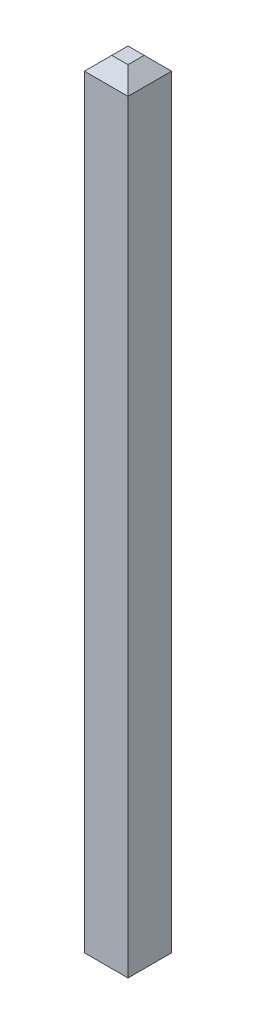
SolidWorks part; units mm, degrees
ref_plane "Alzado" through (0, 0, 0) normal (0, 0, 1) x (1, 0, 0)
ref_plane "Planta" through (0, 0, 0) normal (0, 1, 0) x (1, 0, 0)
ref_plane "Vista lateral" through (0, 0, 0) normal (1, 0, 0) x (0, 0, -1)
sketch "pin_drawing" plane through (0, 0, 0) normal (0, 1, 0) x (1, 0, 0)
  line L1 (0, 0) -> (0.636, 0)
  line L2 (0, 0) -> (0, -0.636)
  line L3 (0, -0.636) -> (0.636, -0.636)
  line L4 (0.636, 0) -> (0.636, -0.636)
extrude "pin" add sketch "pin_drawing" along normal blind 11.54
chamfer "Chamfer2" distance 0.2 angle 45 8 edges at (0, 0, 0.318) (0.318, 0, 0) (0.636, 0, 0.318) (0.318, 0, 0.636) (0.318, 11.54, 0.636) (0.636, 11.54, 0.318) (0.318, 11.54, 0) (0, 11.54, 0.318)
